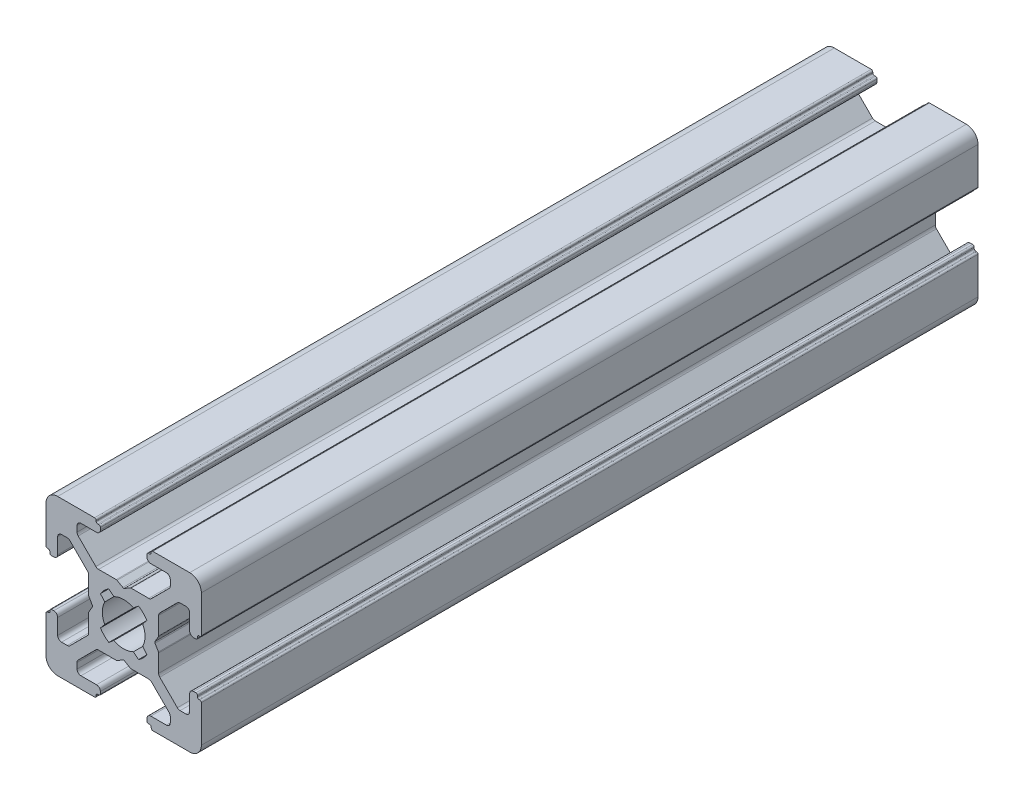
SolidWorks part; units mm, degrees
material "АД31 ГОСТ 4784-2019"
ref_plane "Спереди" through (0, 0, 0) normal (0, 0, 1) x (1, 0, 0)
ref_plane "Сверху" through (0, 0, 0) normal (0, 1, 0) x (1, 0, 0)
ref_plane "Справа" through (0, 0, 0) normal (1, 0, 0) x (0, 0, -1)
sketch "Model" plane through (0, 0, 0) normal (0, 0, 1) x (1, 0, 0)
  line L0 (198.1278, 79.5299) -> (198.6747, 78.8782)
  line L1 (198.6747, 76.3618) -> (198.1278, 75.7101)
  line L2 (199.2061, 74.6304) -> (199.8618, 75.1747)
  line L3 (202.3782, 75.1747) -> (203.0339, 74.6304)
  line L4 (204.1122, 75.7101) -> (203.5653, 76.3618)
  line L5 (203.5653, 78.8782) -> (204.1122, 79.5299)
  line L6 (203.0339, 80.6096) -> (202.3782, 80.0653)
  line L7 (199.8618, 80.0653) -> (199.2061, 80.6096)
  line L8 (197.37, 87.62) -> (192.62, 87.62)
  line L9 (197.57, 87.32) -> (197.57, 87.42)
  line L10 (197.92, 87.12) -> (197.77, 87.12)
  line L11 (198.12, 86.62) -> (198.12, 86.92)
  line L12 (195.62, 86.12) -> (197.62, 86.12)
  line L13 (195.12, 84.8878) -> (195.12, 85.62)
  line L14 (197.5342, 82.2664) -> (195.2664, 84.5342)
  line L15 (200.1664, 82.12) -> (197.8878, 82.12)
  line L16 (201.02, 81.6581) -> (200.2664, 82.0932)
  line L17 (201.9736, 82.0932) -> (201.22, 81.6581)
  line L18 (204.3522, 82.12) -> (202.0736, 82.12)
  line L19 (206.9736, 84.5342) -> (204.7058, 82.2664)
  line L20 (207.12, 85.62) -> (207.12, 84.8878)
  line L21 (204.62, 86.12) -> (206.62, 86.12)
  line L22 (204.12, 86.92) -> (204.12, 86.62)
  line L23 (204.47, 87.12) -> (204.32, 87.12)
  line L24 (204.67, 87.42) -> (204.67, 87.32)
  line L25 (209.62, 87.62) -> (204.87, 87.62)
  line L26 (211.12, 81.37) -> (211.12, 86.12)
  line L27 (210.82, 81.17) -> (210.92, 81.17)
  line L28 (210.62, 80.82) -> (210.62, 80.97)
  line L29 (210.12, 80.62) -> (210.42, 80.62)
  line L30 (209.62, 83.12) -> (209.62, 81.12)
  line L31 (208.3878, 83.62) -> (209.12, 83.62)
  line L32 (205.7664, 81.2058) -> (208.0342, 83.4736)
  line L33 (205.62, 78.5736) -> (205.62, 80.8522)
  line L34 (205.1581, 77.72) -> (205.5932, 78.4736)
  line L35 (205.5932, 76.7664) -> (205.1581, 77.52)
  line L36 (205.62, 74.3878) -> (205.62, 76.6664)
  line L37 (208.0342, 71.7664) -> (205.7664, 74.0342)
  line L38 (209.12, 71.62) -> (208.3878, 71.62)
  line L39 (209.62, 74.12) -> (209.62, 72.12)
  line L40 (210.42, 74.62) -> (210.12, 74.62)
  line L41 (210.62, 74.27) -> (210.62, 74.42)
  line L42 (210.92, 74.07) -> (210.82, 74.07)
  line L43 (211.12, 69.12) -> (211.12, 73.87)
  line L44 (204.87, 67.62) -> (209.62, 67.62)
  line L45 (204.67, 67.92) -> (204.67, 67.82)
  line L46 (204.32, 68.12) -> (204.47, 68.12)
  line L47 (204.12, 68.62) -> (204.12, 68.32)
  line L48 (206.62, 69.12) -> (204.62, 69.12)
  line L49 (207.12, 70.3522) -> (207.12, 69.62)
  line L50 (204.7058, 72.9736) -> (206.9736, 70.7058)
  line L51 (202.0736, 73.12) -> (204.3522, 73.12)
  line L52 (201.22, 73.5819) -> (201.9736, 73.1468)
  line L53 (200.2664, 73.1468) -> (201.02, 73.5819)
  line L54 (197.8878, 73.12) -> (200.1664, 73.12)
  line L55 (195.2664, 70.7058) -> (197.5342, 72.9736)
  line L56 (195.12, 69.62) -> (195.12, 70.3522)
  line L57 (197.62, 69.12) -> (195.62, 69.12)
  line L58 (198.12, 68.32) -> (198.12, 68.62)
  line L59 (197.77, 68.12) -> (197.92, 68.12)
  line L60 (197.57, 67.82) -> (197.57, 67.92)
  line L61 (192.62, 67.62) -> (197.37, 67.62)
  line L62 (191.12, 73.87) -> (191.12, 69.12)
  line L63 (191.42, 74.07) -> (191.32, 74.07)
  line L64 (191.62, 74.42) -> (191.62, 74.27)
  line L65 (192.12, 74.62) -> (191.82, 74.62)
  line L66 (192.62, 72.12) -> (192.62, 74.12)
  line L67 (193.8522, 71.62) -> (193.12, 71.62)
  line L68 (196.4736, 74.0342) -> (194.2058, 71.7664)
  line L69 (196.62, 76.6664) -> (196.62, 74.3878)
  line L70 (197.0819, 77.52) -> (196.6468, 76.7664)
  line L71 (196.6468, 78.4736) -> (197.0819, 77.72)
  line L72 (196.62, 80.8522) -> (196.62, 78.5736)
  line L73 (194.2058, 83.4736) -> (196.4736, 81.2058)
  line L74 (193.12, 83.62) -> (193.8522, 83.62)
  line L75 (192.62, 81.12) -> (192.62, 83.12)
  line L76 (191.82, 80.62) -> (192.12, 80.62)
  line L77 (191.62, 80.97) -> (191.62, 80.82)
  line L78 (191.32, 81.17) -> (191.42, 81.17)
  line L79 (191.12, 86.12) -> (191.12, 81.37)
  arc A0 (198.6747, 78.8782) -> (198.6747, 76.3618) centre (201.12, 77.62) ccw
  arc A1 (198.1278, 75.7101) -> (199.2061, 74.6304) centre (201.12, 77.62) ccw
  arc A2 (199.8618, 75.1747) -> (202.3782, 75.1747) centre (201.12, 77.62) ccw
  arc A3 (203.0339, 74.6304) -> (204.1122, 75.7101) centre (201.12, 77.62) ccw
  arc A4 (203.5653, 76.3618) -> (203.5653, 78.8782) centre (201.12, 77.62) ccw
  arc A5 (204.1122, 79.5299) -> (203.0339, 80.6096) centre (201.12, 77.62) ccw
  arc A6 (202.3782, 80.0653) -> (199.8618, 80.0653) centre (201.12, 77.62) ccw
  arc A7 (199.2061, 80.6096) -> (198.1278, 79.5299) centre (201.12, 77.62) ccw
  arc A8 (197.57, 87.42) -> (197.37, 87.62) centre (197.37, 87.42) ccw
  arc A9 (197.57, 87.32) -> (197.77, 87.12) centre (197.77, 87.32) ccw
  arc A10 (198.12, 86.92) -> (197.92, 87.12) centre (197.92, 86.92) ccw
  arc A11 (197.62, 86.12) -> (198.12, 86.62) centre (197.62, 86.62) ccw
  arc A12 (195.62, 86.12) -> (195.12, 85.62) centre (195.62, 85.62) ccw
  arc A13 (195.12, 84.8878) -> (195.2664, 84.5342) centre (195.62, 84.8878) ccw
  arc A14 (197.5342, 82.2664) -> (197.8878, 82.12) centre (197.8878, 82.62) ccw
  arc A15 (200.2664, 82.0932) -> (200.1664, 82.12) centre (200.1664, 81.92) ccw
  arc A16 (201.02, 81.6581) -> (201.22, 81.6581) centre (201.12, 81.8313) ccw
  arc A17 (202.0736, 82.12) -> (201.9736, 82.0932) centre (202.0736, 81.92) ccw
  arc A18 (204.3522, 82.12) -> (204.7058, 82.2664) centre (204.3522, 82.62) ccw
  arc A19 (206.9736, 84.5342) -> (207.12, 84.8878) centre (206.62, 84.8878) ccw
  arc A20 (207.12, 85.62) -> (206.62, 86.12) centre (206.62, 85.62) ccw
  arc A21 (204.12, 86.62) -> (204.62, 86.12) centre (204.62, 86.62) ccw
  arc A22 (204.32, 87.12) -> (204.12, 86.92) centre (204.32, 86.92) ccw
  arc A23 (204.47, 87.12) -> (204.67, 87.32) centre (204.47, 87.32) ccw
  arc A24 (204.87, 87.62) -> (204.67, 87.42) centre (204.87, 87.42) ccw
  arc A25 (211.12, 86.12) -> (209.62, 87.62) centre (209.62, 86.12) ccw
  arc A26 (210.92, 81.17) -> (211.12, 81.37) centre (210.92, 81.37) ccw
  arc A27 (210.82, 81.17) -> (210.62, 80.97) centre (210.82, 80.97) ccw
  arc A28 (210.42, 80.62) -> (210.62, 80.82) centre (210.42, 80.82) ccw
  arc A29 (209.62, 81.12) -> (210.12, 80.62) centre (210.12, 81.12) ccw
  arc A30 (209.62, 83.12) -> (209.12, 83.62) centre (209.12, 83.12) ccw
  arc A31 (208.3878, 83.62) -> (208.0342, 83.4736) centre (208.3878, 83.12) ccw
  arc A32 (205.7664, 81.2058) -> (205.62, 80.8522) centre (206.12, 80.8522) ccw
  arc A33 (205.5932, 78.4736) -> (205.62, 78.5736) centre (205.42, 78.5736) ccw
  arc A34 (205.1581, 77.72) -> (205.1581, 77.52) centre (205.3313, 77.62) ccw
  arc A35 (205.62, 76.6664) -> (205.5932, 76.7664) centre (205.42, 76.6664) ccw
  arc A36 (205.62, 74.3878) -> (205.7664, 74.0342) centre (206.12, 74.3878) ccw
  arc A37 (208.0342, 71.7664) -> (208.3878, 71.62) centre (208.3878, 72.12) ccw
  arc A38 (209.12, 71.62) -> (209.62, 72.12) centre (209.12, 72.12) ccw
  arc A39 (210.12, 74.62) -> (209.62, 74.12) centre (210.12, 74.12) ccw
  arc A40 (210.62, 74.42) -> (210.42, 74.62) centre (210.42, 74.42) ccw
  arc A41 (210.62, 74.27) -> (210.82, 74.07) centre (210.82, 74.27) ccw
  arc A42 (211.12, 73.87) -> (210.92, 74.07) centre (210.92, 73.87) ccw
  arc A43 (209.62, 67.62) -> (211.12, 69.12) centre (209.62, 69.12) ccw
  arc A44 (204.67, 67.82) -> (204.87, 67.62) centre (204.87, 67.82) ccw
  arc A45 (204.67, 67.92) -> (204.47, 68.12) centre (204.47, 67.92) ccw
  arc A46 (204.12, 68.32) -> (204.32, 68.12) centre (204.32, 68.32) ccw
  arc A47 (204.62, 69.12) -> (204.12, 68.62) centre (204.62, 68.62) ccw
  arc A48 (206.62, 69.12) -> (207.12, 69.62) centre (206.62, 69.62) ccw
  arc A49 (207.12, 70.3522) -> (206.9736, 70.7058) centre (206.62, 70.3522) ccw
  arc A50 (204.7058, 72.9736) -> (204.3522, 73.12) centre (204.3522, 72.62) ccw
  arc A51 (201.9736, 73.1468) -> (202.0736, 73.12) centre (202.0736, 73.32) ccw
  arc A52 (201.22, 73.5819) -> (201.02, 73.5819) centre (201.12, 73.4087) ccw
  arc A53 (200.1664, 73.12) -> (200.2664, 73.1468) centre (200.1664, 73.32) ccw
  arc A54 (197.8878, 73.12) -> (197.5342, 72.9736) centre (197.8878, 72.62) ccw
  arc A55 (195.2664, 70.7058) -> (195.12, 70.3522) centre (195.62, 70.3522) ccw
  arc A56 (195.12, 69.62) -> (195.62, 69.12) centre (195.62, 69.62) ccw
  arc A57 (198.12, 68.62) -> (197.62, 69.12) centre (197.62, 68.62) ccw
  arc A58 (197.92, 68.12) -> (198.12, 68.32) centre (197.92, 68.32) ccw
  arc A59 (197.77, 68.12) -> (197.57, 67.92) centre (197.77, 67.92) ccw
  arc A60 (197.37, 67.62) -> (197.57, 67.82) centre (197.37, 67.82) ccw
  arc A61 (191.12, 69.12) -> (192.62, 67.62) centre (192.62, 69.12) ccw
  arc A62 (191.32, 74.07) -> (191.12, 73.87) centre (191.32, 73.87) ccw
  arc A63 (191.42, 74.07) -> (191.62, 74.27) centre (191.42, 74.27) ccw
  arc A64 (191.82, 74.62) -> (191.62, 74.42) centre (191.82, 74.42) ccw
  arc A65 (192.62, 74.12) -> (192.12, 74.62) centre (192.12, 74.12) ccw
  arc A66 (192.62, 72.12) -> (193.12, 71.62) centre (193.12, 72.12) ccw
  arc A67 (193.8522, 71.62) -> (194.2058, 71.7664) centre (193.8522, 72.12) ccw
  arc A68 (196.4736, 74.0342) -> (196.62, 74.3878) centre (196.12, 74.3878) ccw
  arc A69 (196.6468, 76.7664) -> (196.62, 76.6664) centre (196.82, 76.6664) ccw
  arc A70 (197.0819, 77.52) -> (197.0819, 77.72) centre (196.9087, 77.62) ccw
  arc A71 (196.62, 78.5736) -> (196.6468, 78.4736) centre (196.82, 78.5736) ccw
  arc A72 (196.62, 80.8522) -> (196.4736, 81.2058) centre (196.12, 80.8522) ccw
  arc A73 (194.2058, 83.4736) -> (193.8522, 83.62) centre (193.8522, 83.12) ccw
  arc A74 (193.12, 83.62) -> (192.62, 83.12) centre (193.12, 83.12) ccw
  arc A75 (192.12, 80.62) -> (192.62, 81.12) centre (192.12, 81.12) ccw
  arc A76 (191.62, 80.82) -> (191.82, 80.62) centre (191.82, 80.82) ccw
  arc A77 (191.62, 80.97) -> (191.42, 81.17) centre (191.42, 80.97) ccw
  arc A78 (191.12, 81.37) -> (191.32, 81.17) centre (191.32, 81.37) ccw
  arc A79 (192.62, 87.62) -> (191.12, 86.12) centre (192.62, 86.12) ccw
extrude "Бобышка-Вытянуть1" add sketch "Model" along normal blind 100
